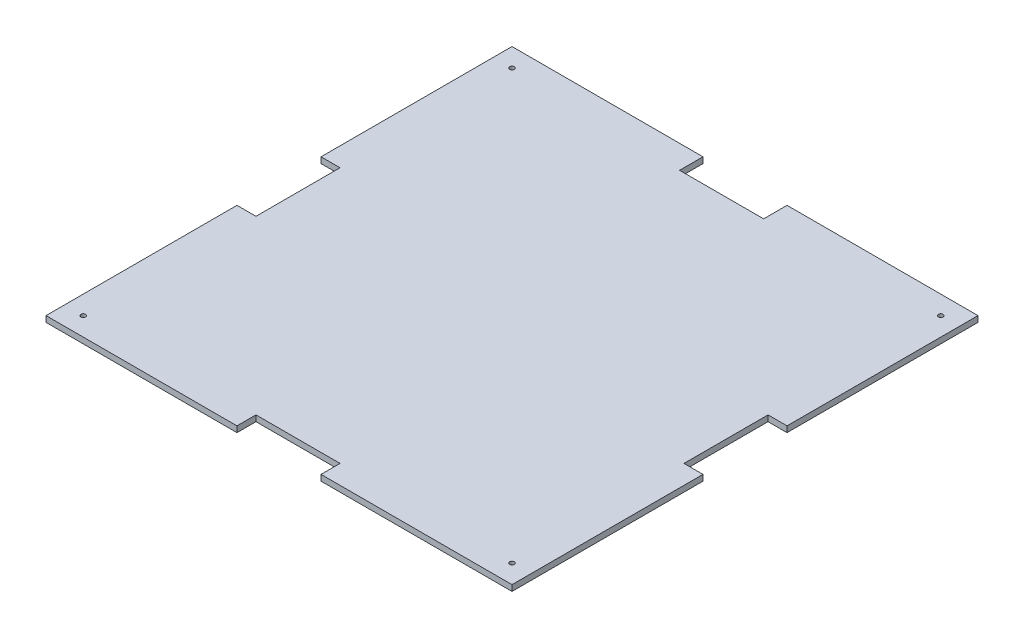
SolidWorks part; units mm, degrees
ref_plane "Front Plane" through (0, 0, 0) normal (0, 0, 1) x (1, 0, 0)
ref_plane "Top Plane" through (0, 0, 0) normal (0, 1, 0) x (1, 0, 0)
ref_plane "Right Plane" through (0, 0, 0) normal (1, 0, 0) x (0, 0, -1)
sketch "Sketch2" plane through (0, 0, 0) normal (0, 1, 0) x (1, 0, 0)
  line L1 (-125, -125) -> (125, -125)
  line L2 (-125, -125) -> (-125, 125)
  line L3 (-125, 125) -> (125, 125)
  line L4 (125, -125) -> (125, 125)
  line L5 (-125, -125) -> (125, 125) construction
  line L6 (-125, 125) -> (125, -125) construction
  point P0 (0, 0)
  dimension "D2" = 250
extrude "Base" add sketch "Sketch2" along normal blind 3.175
sketch "Sketch3" plane through (0, 3.175, 0) normal (0, 1, 0) x (1, 0, 0)
  line L0 (-125, 0) -> (125, 0) construction
  line L1 (-125, 125) -> (-125, -125) construction
  line L2 (125, -125) -> (125, 125) construction
  line L3 (-43.75, 125) -> (-43.75, -125) construction
  line L4 (125, 125) -> (-125, 125) construction
  line L5 (-125, -125) -> (125, -125) construction
  line L6 (0, 125) -> (0, -125) construction
  line L11 (-48.05, 28) -> (-39.45, 28)
  line L12 (-48.05, 28) -> (-48.05, 43.35)
  line L13 (-48.05, 43.35) -> (-39.45, 43.35)
  line L14 (-39.45, 28) -> (-39.45, 43.35)
  line L15 (-48.05, 28) -> (-39.45, 43.35) construction
  line L16 (-48.05, 43.35) -> (-39.45, 28) construction
  line L21 (-48.05, -43.35) -> (-39.45, -43.35)
  line L22 (-48.05, -43.35) -> (-48.05, -28)
  line L23 (-48.05, -28) -> (-39.45, -28)
  line L24 (-39.45, -43.35) -> (-39.45, -28)
  line L25 (-48.05, -43.35) -> (-39.45, -28) construction
  line L26 (-48.05, -28) -> (-39.45, -43.35) construction
  line L27 (48.05, -28) -> (39.45, -28)
  line L28 (39.45, -43.35) -> (39.45, -28)
  line L29 (48.05, -43.35) -> (39.45, -43.35)
  line L30 (48.05, -43.35) -> (48.05, -28)
  line L31 (48.05, 43.35) -> (39.45, 43.35)
  line L32 (39.45, 28) -> (39.45, 43.35)
  line L33 (48.05, 28) -> (39.45, 28)
  line L34 (48.05, 28) -> (48.05, 43.35)
  point P12 (-43.75, 35.675)
  point P17 (-43.75, -35.675)
  dimension "D1" = 43.75
  dimension "D2" = 8.6
  dimension "D3" = 15.35
  dimension "D4" = 56
  dimension "D5" = 28
sketch "Sketch4" plane through (0, 3.175, 0) normal (0, 1, 0) x (1, 0, 0)
  line L0 (0, 125) -> (0, -125) construction
  line L1 (125, 125) -> (-125, 125) construction
  line L2 (-125, -125) -> (125, -125) construction
  line L3 (-125, 0) -> (125, 0) construction
  line L4 (-125, 125) -> (-125, -125) construction
  line L5 (125, -125) -> (125, 125) construction
  line L7 (-22.55, 137.55) -> (22.55, 137.55)
  line L8 (-22.55, 137.55) -> (-22.55, 112.45)
  line L9 (-22.55, 112.45) -> (22.55, 112.45)
  line L10 (22.55, 137.55) -> (22.55, 112.45)
  line L11 (-22.55, 137.55) -> (22.55, 112.45) construction
  line L12 (-22.55, 112.45) -> (22.55, 137.55) construction
  line L41 (-114.8105, -22.55) -> (-135.1895, -22.55)
  line L42 (-114.8105, -22.55) -> (-114.8105, 22.55)
  line L43 (-114.8105, 22.55) -> (-135.1895, 22.55)
  line L44 (-135.1895, -22.55) -> (-135.1895, 22.55)
  line L45 (-114.8105, -22.55) -> (-135.1895, 22.55) construction
  line L46 (-114.8105, 22.55) -> (-135.1895, -22.55) construction
  line L47 (114.8105, -22.55) -> (135.1895, -22.55)
  line L48 (114.8105, -22.55) -> (114.8105, 22.55)
  line L49 (114.8105, 22.55) -> (135.1895, 22.55)
  line L50 (135.1895, -22.55) -> (135.1895, 22.55)
  line L51 (114.8105, -22.55) -> (135.1895, 22.55) construction
  line L52 (114.8105, 22.55) -> (135.1895, -22.55) construction
  line L53 (22.55, -114.8105) -> (-22.55, -114.8105)
  line L54 (22.55, -114.8105) -> (22.55, -135.1895)
  line L55 (22.55, -135.1895) -> (-22.55, -135.1895)
  line L56 (-22.55, -114.8105) -> (-22.55, -135.1895)
  line L57 (22.55, -114.8105) -> (-22.55, -135.1895) construction
  line L58 (22.55, -135.1895) -> (-22.55, -114.8105) construction
  point P31 (-25, 25)
  point P32 (25, -25)
  dimension "D1" = 25.1
  dimension "D2" = 45.1
extrude "Jigsaw" cut sketch "Sketch4" against normal blind 10
hole_wizard "Standoff Holes" positions "Sketch5" profile "Sketch6" tap size "M3" standard "ISO" end condition through all
sketch "Sketch5" plane through (0, 3.175, 0) normal (0, 1, 0) x (1, 0, 0)
  line L0 (-22.55, 125) -> (-125, 125) construction
  line L1 (-125, 125) -> (-125, 22.55) construction
  point P0 (-115, 115)
  dimension "D1" = 10
  dimension "D2" = 10
sketch "Sketch6" plane through (-115, 3.175, -115) normal (1, 0, 0) x (0, 0, 1)
  line L0 (0, 0) -> (0, 3.175)
  line L1 (0, 3.175) -> (1.25, 3.175)
  line L2 (1.25, 3.175) -> (1.25, 0)
  line L5 (1.25, 0) -> (0, 0)
  line L11 (0, -6.35) -> (0, 107.95) construction
  dimension "Thru Tap Drill Dia." = 2.5
  dimension "Thru Tap Drill Depth" = 3.175
cosmetic thread "Hole Thread9" parameters "D2"=3
hole_wizard "Standoff Holes 2" positions "Sketch7" profile "Sketch8" tap size "M3" standard "ISO" end condition through all
sketch "Sketch7" plane through (0, 3.175, 0) normal (0, 1, 0) x (1, 0, 0)
  line L0 (-125, -125) -> (-22.55, -125) construction
  line L1 (-125, -22.55) -> (-125, -125) construction
  line L2 (125, -125) -> (125, -22.55) construction
  line L3 (22.55, -125) -> (125, -125) construction
  line L4 (125, 22.55) -> (125, 125) construction
  line L5 (125, 125) -> (22.55, 125) construction
  point P0 (115, 115)
  point P2 (115, -115)
  point P4 (-115, -115)
  dimension "D1" = 10
  dimension "D2" = 10
  dimension "D3" = 10
  dimension "D4" = 10
  dimension "D5" = 10
  dimension "D6" = 10
sketch "Sketch8" plane through (115, 3.175, -115) normal (1, 0, 0) x (0, 0, 1)
  line L0 (0, 0) -> (0, 3.175)
  line L1 (0, 3.175) -> (1.25, 3.175)
  line L2 (1.25, 3.175) -> (1.25, 0)
  line L5 (1.25, 0) -> (0, 0)
  line L11 (0, -6.35) -> (0, 107.95) construction
  dimension "Thru Tap Drill Dia." = 2.5
  dimension "Thru Tap Drill Depth" = 3.175
cosmetic thread "Hole Thread11" parameters "D2"=3
cosmetic thread "Hole Thread12" parameters "D2"=3
cosmetic thread "Hole Thread15" parameters "D2"=3
